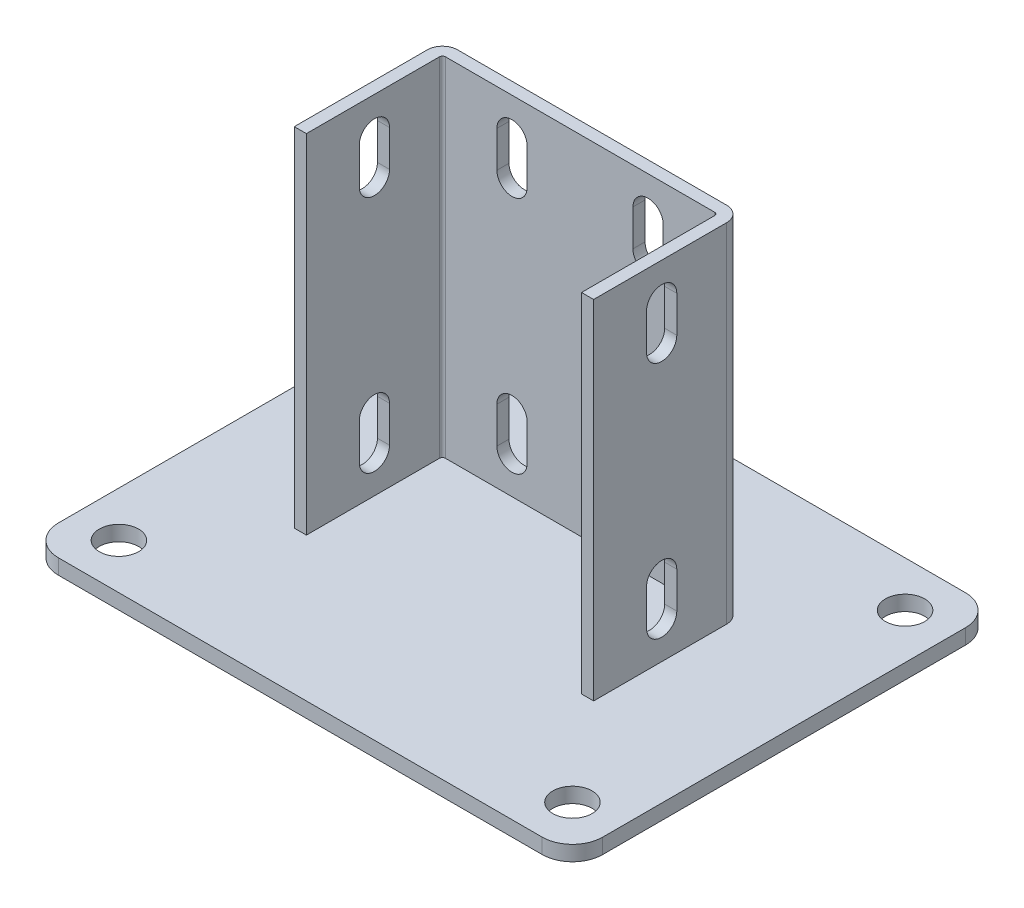
SolidWorks part; units mm, degrees
material "Ст3пс ГОСТ 380-2005"
ref_plane "Спереди" through (0, 0, 0) normal (0, 0, 1) x (1, 0, 0)
ref_plane "Сверху" through (0, 0, 0) normal (0, 1, 0) x (1, 0, 0)
ref_plane "Справа" through (0, 0, 0) normal (1, 0, 0) x (0, 0, -1)
sketch "Эскиз2" plane through (0, 0, 0) normal (0, 1, 0) x (1, 0, 0)
  line L1 (-90, -70) -> (90, -70)
  line L2 (-90, -70) -> (-90, 70)
  line L3 (-90, 70) -> (90, 70)
  line L4 (90, -70) -> (90, 70)
  line L5 (-90, -70) -> (90, 70) construction
  line L6 (-90, 70) -> (90, -70) construction
  point P0 (0, 0)
  dimension "D1" = 140
  dimension "D2" = 180
extrude "Бобышка-Вытянуть1" add sketch "Эскиз2" along normal blind 5
sketch "Эскиз3" plane through (0, 5, 0) normal (0, 1, 0) x (1, 0, 0)
  line L0 (-45.5, -22.5) -> (-45.5, 22.5)
  line L1 (-45.5, 22.5) -> (45.5, 22.5)
  line L2 (45.5, 22.5) -> (45.5, -22.5)
  point P2 (0, 22.5)
  point P5 (-45.5, 0)
  dimension "D2" = 91
  dimension "D3" = 45
extrude "Вытянуть-Тонкостенный1" add sketch "Эскиз3" along normal offset from surface (115 mm away) 120 thin up to face at (0, 0, 0) thin type one direction reverse wall 4
sketch "Эскиз4" plane through (0, 0, 0) normal (1, 0, 0) x (0, 0, -1)
  line L0 (26.5, 71.684) -> (65, 5)
  line L1 (26.5, 120) -> (26.5, 5) construction
  line L2 (-70, 5) -> (70, 5) construction
  line L3 (65, 5) -> (26.5, 5)
  line L4 (26.5, 5) -> (26.5, 71.684)
  line L5 (70, 5) -> (70, 0) construction
  dimension "D1" = 30
  dimension "D2" = 5
extrude "Бобышка-Вытянуть2" add sketch "Эскиз4" along normal mid plane 4
sketch "Эскиз5" plane through (49.5, 0, 0) normal (1, 0, 0) x (0, 0, -1)
  line L0 (0, 108) -> (0, 96) construction
  line L1 (5, 108) -> (5, 96)
  line L2 (-5, 108) -> (-5, 96)
  line L3 (0, 29) -> (0, 17) construction
  line L4 (5, 29) -> (5, 17)
  line L5 (-5, 29) -> (-5, 17)
  line L6 (-22.5, 120) -> (21.5, 120) construction
  line L7 (-70, 5) -> (70, 5) construction
  arc A0 (5, 108) -> (-5, 108) centre (0, 108) ccw
  arc A1 (-5, 96) -> (5, 96) centre (0, 96) ccw
  arc A2 (5, 29) -> (-5, 29) centre (0, 29) ccw
  arc A3 (-5, 17) -> (5, 17) centre (0, 17) ccw
  point P3 (0, 102)
  point P8 (0, 23)
  dimension "D2" = 12
  dimension "D4" = 12
  dimension "D1" = 10
  dimension "D3" = 12
extrude "Вырез-Вытянуть1" cut sketch "Эскиз5" against normal through all
sketch "Эскиз6" plane through (0, 5, 0) normal (0, 1, 0) x (1, 0, 0)
  line L0 (-90, 70) -> (-90, -70) construction
  line L1 (75, -55) -> (-75, -55) construction
  line L2 (75, -55) -> (75, 55) construction
  line L3 (75, 55) -> (-75, 55) construction
  line L4 (-75, -55) -> (-75, 55) construction
  line L5 (75, -55) -> (-75, 55) construction
  line L6 (75, 55) -> (-75, -55) construction
  line L7 (90, 70) -> (-90, 70) construction
  circle A0 centre (-75, 55) radius 6.5
  circle A1 centre (-75, -55) radius 6.5
  circle A2 centre (75, 55) radius 6.5
  circle A3 centre (75, -55) radius 6.5
  point P0 (0, 0)
  dimension "D1" = 13
  dimension "D2" = 15
  dimension "D3" = 15
extrude "Вырез-Вытянуть2" cut sketch "Эскиз6" against normal through all
fillet "Скругление1" radius 10 4 edges at (90, 2.5, 70) (-90, 2.5, 70) (-90, 2.5, -70) (90, 2.5, -70)
sketch "Эскиз8" plane through (0, 0, -26.5) normal (0, 0, -1) x (-1, 0, 0)
  line L0 (-22.5, 108) -> (-22.5, 96) construction
  line L1 (-17.5, 108) -> (-17.5, 96)
  line L2 (-27.5, 108) -> (-27.5, 96)
  line L3 (-22.5, 29) -> (-22.5, 17) construction
  line L4 (-17.5, 29) -> (-17.5, 17)
  line L5 (-27.5, 29) -> (-27.5, 17)
  line L6 (-44.5, 120) -> (44.5, 120) construction
  line L7 (-80, 5) -> (80, 5) construction
  line L8 (0, 0) -> (0, 120) construction
  line L9 (-80, 0) -> (80, 0) construction
  line L10 (22.5, 108) -> (22.5, 96) construction
  line L11 (17.5, 108) -> (17.5, 96)
  line L12 (27.5, 108) -> (27.5, 96)
  line L13 (22.5, 29) -> (22.5, 17) construction
  line L14 (17.5, 29) -> (17.5, 17)
  line L15 (27.5, 29) -> (27.5, 17)
  arc A0 (-17.5, 108) -> (-27.5, 108) centre (-22.5, 108) ccw
  arc A1 (-27.5, 96) -> (-17.5, 96) centre (-22.5, 96) ccw
  arc A2 (-17.5, 29) -> (-27.5, 29) centre (-22.5, 29) ccw
  arc A3 (-27.5, 17) -> (-17.5, 17) centre (-22.5, 17) ccw
  arc A4 (17.5, 108) -> (27.5, 108) centre (22.5, 108) cw
  arc A5 (27.5, 96) -> (17.5, 96) centre (22.5, 96) cw
  arc A6 (17.5, 29) -> (27.5, 29) centre (22.5, 29) cw
  arc A7 (27.5, 17) -> (17.5, 17) centre (22.5, 17) cw
  point P2 (-22.5, 102)
  point P7 (-22.5, 23)
  point P24 (22.5, 102)
  point P31 (22.5, 23)
  dimension "D3" = 12
  dimension "D4" = 12
  dimension "D1" = 10
  dimension "D2" = 12
  dimension "D5" = 35
extrude "Вырез-Вытянуть3" cut sketch "Эскиз8" against normal up to next
